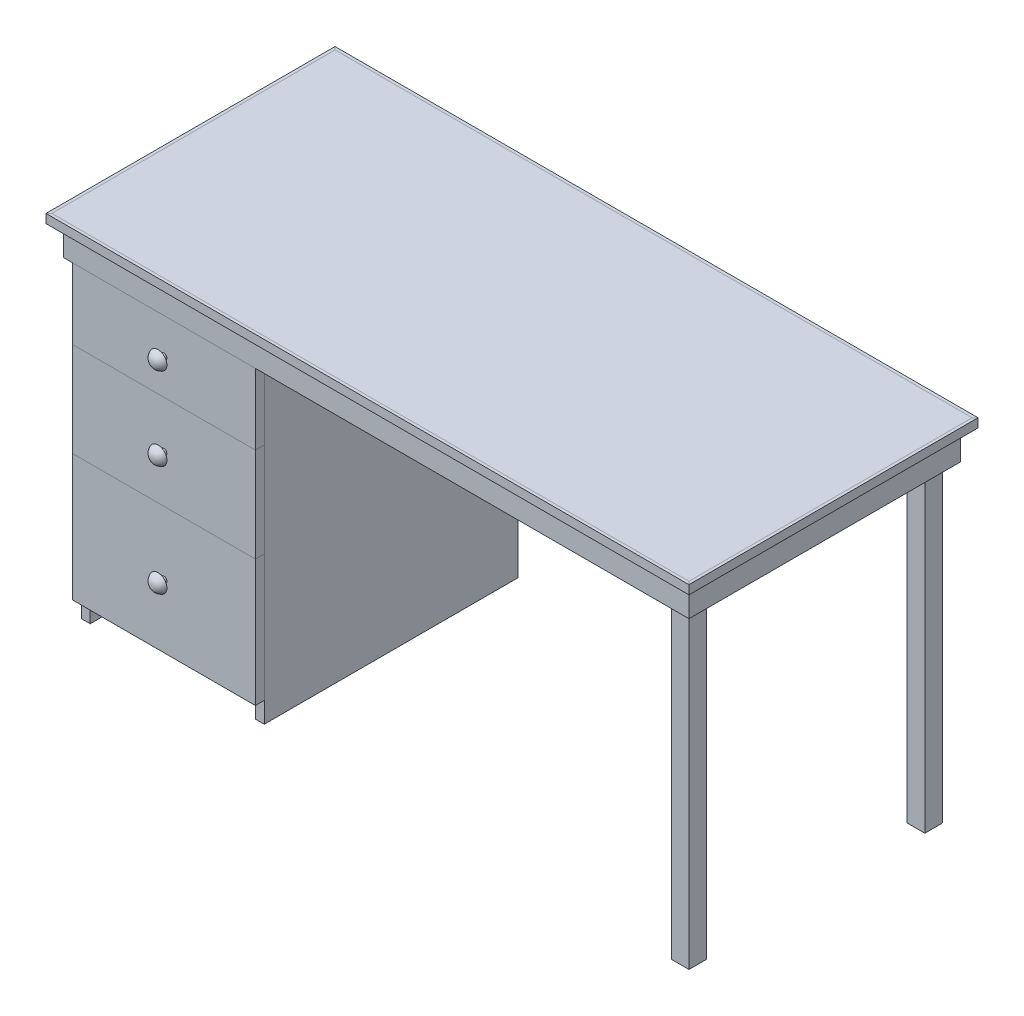
SolidWorks part; units mm, degrees
material "Oak"
ref_plane "Front Plane" through (0, 0, 0) normal (0, 0, 1) x (1, 0, 0)
ref_plane "Top Plane" through (0, 0, 0) normal (0, 1, 0) x (1, 0, 0)
ref_plane "Right Plane" through (0, 0, 0) normal (1, 0, 0) x (0, 0, -1)
sketch "Sketch1" plane through (0, 0, 0) normal (0, 1, 0) x (1, 0, 0)
  line L0 (-685.8, 304.8) -> (685.8, -304.8) construction
  line L1 (-685.8, 304.8) -> (685.8, 304.8)
  line L2 (-685.8, 304.8) -> (-685.8, -304.8)
  line L3 (-685.8, -304.8) -> (685.8, -304.8)
  line L4 (685.8, 304.8) -> (685.8, -304.8)
  dimension "D1" = 609.6
  dimension "D2" = 1371.6
extrude "Top" add sketch "Sketch1" against normal blind 19.05
sketch "Sketch26" plane through (0, 0, 0) normal (0, 1, 0) x (1, 0, 0)
  line L0 (-692.15, -311.15) -> (-685.8, -304.8)
  line L1 (-685.8, -304.8) -> (685.8, -304.8)
  line L2 (685.8, -304.8) -> (692.15, -311.15)
  line L3 (692.15, -311.15) -> (-692.15, -311.15)
  line L5 (-685.8, 304.8) -> (-685.8, -304.8) construction
  line L7 (685.8, -304.8) -> (685.8, 304.8) construction
  line L8 (-685.8, 0) -> (685.8, 0) construction
  line L9 (692.15, 311.15) -> (-692.15, 311.15)
  line L10 (685.8, 304.8) -> (692.15, 311.15)
  line L11 (-685.8, 304.8) -> (685.8, 304.8)
  line L12 (-692.15, 311.15) -> (-685.8, 304.8)
  dimension "D1" = 135
  dimension "D2" = 135
  dimension "D3" = 6.35
extrude "Top Siding Front and Back" add sketch "Sketch26" against normal blind 19.05 separate body
sketch "Sketch27" plane through (0, 0, 0) normal (0, 1, 0) x (1, 0, 0)
  line L0 (-692.15, 311.15) -> (-692.15, -311.15)
  line L1 (-692.15, -311.15) -> (-685.8, -304.8)
  line L2 (-685.8, 304.8) -> (-692.15, 311.15)
  line L3 (0, 311.15) -> (0, -311.15) construction
  line L4 (692.15, 311.15) -> (-692.15, 311.15) construction
  line L5 (-692.15, -311.15) -> (692.15, -311.15) construction
  line L6 (-685.8, 304.8) -> (-685.8, -304.8) construction
  line L7 (-685.8, 304.8) -> (-685.8, -304.8)
  line L8 (685.8, 304.8) -> (685.8, -304.8)
  line L9 (685.8, 304.8) -> (692.15, 311.15)
  line L10 (692.15, -311.15) -> (685.8, -304.8)
  line L11 (692.15, 311.15) -> (692.15, -311.15)
extrude "Top Siding Sides" add sketch "Sketch27" against normal blind 19.05 separate body
sketch "Sketch2" plane through (0, -19.05, 0) normal (0, -1, 0) x (1, 0, 0)
  line L0 (-673.1, 292.1) -> (-654.05, 273.05)
  line L1 (-654.05, 273.05) -> (654.05, 273.05)
  line L2 (654.05, 273.05) -> (673.1, 292.1)
  line L3 (673.1, 292.1) -> (-673.1, 292.1)
  line L4 (-685.8, 304.8) -> (-459.3839, 78.3839) construction
  line L5 (685.8, 304.8) -> (524.6776, 143.6776) construction
  line L6 (-685.8, 304.8) -> (685.8, 304.8) construction
  line L7 (685.8, 304.8) -> (685.8, -304.8) construction
  line L8 (654.05, -273.05) -> (673.1, -292.1)
  line L9 (-673.1, -292.1) -> (-654.05, -273.05)
  line L10 (673.1, -292.1) -> (-673.1, -292.1)
  line L11 (-685.8, 0) -> (685.8, 0) construction
  line L12 (-685.8, -304.8) -> (-685.8, 304.8) construction
  line L13 (-654.05, -273.05) -> (654.05, -273.05)
  dimension "D1" = 1346.2
  dimension "D2" = 19.05
  dimension "D3" = 45
  dimension "D4" = 45
extrude "Long Side Rails" add sketch "Sketch2" along normal blind 63.5 separate body
sketch "Sketch3" plane through (0, -19.05, 0) normal (0, -1, 0) x (1, 0, 0)
  line L0 (0, -304.8) -> (0, 304.8) construction
  line L2 (-685.8, 304.8) -> (685.8, 304.8) construction
  line L3 (685.8, -304.8) -> (-685.8, -304.8) construction
  line L4 (-673.1, 292.1) -> (-654.05, 273.05) construction
  line L5 (-673.1, 292.1) -> (-654.05, 273.05)
  line L6 (-673.1, 292.1) -> (-673.1, -292.1)
  line L7 (-654.05, 273.05) -> (-654.05, -273.05)
  line L9 (-654.05, -273.05) -> (-673.1, -292.1) construction
  line L10 (654.05, -273.05) -> (673.1, -292.1)
  line L11 (673.1, 292.1) -> (673.1, -292.1)
  line L12 (673.1, 292.1) -> (654.05, 273.05)
  line L13 (654.05, 273.05) -> (654.05, -273.05)
  line L14 (-654.05, -273.05) -> (-673.1, -292.1)
extrude "Short Side Rails" add sketch "Sketch3" along normal blind 63.5 separate body
sketch "Sketch4" plane through (0, -19.05, 0) normal (0, -1, 0) x (1, 0, 0)
  line L0 (-685.8, 0) -> (685.8, 0) construction
  line L1 (654.05, 273.05) -> (615.95, 273.05)
  line L2 (654.05, 273.05) -> (654.05, 234.95)
  line L3 (654.05, 234.95) -> (615.95, 234.95)
  line L4 (615.95, 273.05) -> (615.95, 234.95)
  line L5 (-685.8, -304.8) -> (-685.8, 304.8) construction
  line L6 (685.8, 304.8) -> (685.8, -304.8) construction
  line L7 (654.05, -234.95) -> (615.95, -234.95)
  line L8 (654.05, -273.05) -> (654.05, -234.95)
  line L9 (654.05, -273.05) -> (615.95, -273.05)
  line L10 (615.95, -273.05) -> (615.95, -234.95)
  dimension "D1" = 38.1
extrude "Legs" add sketch "Sketch4" along normal blind 736.6
sketch "Sketch5" plane through (0, -19.05, 0) normal (0, -1, 0) x (1, 0, 0)
  line L0 (615.95, -273.05) -> (-654.05, -273.05) construction
  line L1 (-654.05, 273.05) -> (-635, 273.05)
  line L2 (-654.05, 273.05) -> (-654.05, -273.05)
  line L3 (-654.05, -273.05) -> (-635, -273.05)
  line L4 (-635, 273.05) -> (-635, -273.05)
  line L5 (-457.2, 304.8) -> (-457.2, -304.8) construction
  line L6 (-685.8, 304.8) -> (685.8, 304.8) construction
  line L7 (685.8, -304.8) -> (-685.8, -304.8) construction
  line L8 (-260.35, -273.05) -> (-279.4, -273.05)
  line L9 (-260.35, 273.05) -> (-279.4, 273.05)
  line L10 (-260.35, 273.05) -> (-260.35, -273.05)
  line L11 (-279.4, 273.05) -> (-279.4, -273.05)
  dimension "D1" = 19.05
  dimension "D2" = 196.85
extrude "Case Sides" add sketch "Sketch5" along normal blind 736.6 separate body
sketch "Sketch6" plane through (0, -19.05, 0) normal (0, -1, 0) x (1, 0, 0)
  line L4 (-635, -273.05) -> (-635, 273.05) construction
  line L5 (-279.4, 273.05) -> (-279.4, -273.05) construction
  line L7 (-635, -273.05) -> (-635, 273.05)
  line L8 (-279.4, 273.05) -> (-279.4, -273.05)
  line L9 (-635, 273.05) -> (-279.4, 273.05)
  line L10 (-635, -273.05) -> (-279.4, -273.05)
extrude "Case Top" add sketch "Sketch6" along normal blind 19.05 separate body
ref_plane "Case Bottom Plane" through (0, -685.8, 0) normal (0, -1, 0) x (-1, 0, 0)
sketch "Sketch7" plane through (0, -685.8, 0) normal (0, -1, 0) x (-1, 0, 0)
  line L0 (635, -273.05) -> (279.4, -273.05)
  line L1 (279.4, -273.05) -> (279.4, 273.05)
  line L2 (279.4, 273.05) -> (635, 273.05)
  line L3 (635, 273.05) -> (635, -273.05)
extrude "Case Bottom" add sketch "Sketch7" along normal blind 19.05 separate body
sketch "Sketch8" plane through (0, -19.05, 0) normal (0, -1, 0) x (1, 0, 0)
  line L0 (577.85, 273.05) -> (654.05, 196.85)
  line L1 (-654.05, 273.05) -> (615.95, 273.05) construction
  line L2 (654.05, 234.95) -> (654.05, -234.95) construction
  line L3 (550.9092, 273.05) -> (654.05, 169.9092)
  line L4 (577.85, 273.05) -> (550.9092, 273.05)
  line L5 (654.05, 196.85) -> (654.05, 169.9092)
  line L6 (0, 0) -> (685.8, 0) construction
  line L7 (685.8, 304.8) -> (685.8, -304.8) construction
  line L8 (654.05, -196.85) -> (654.05, -169.9092)
  line L9 (550.9092, -273.05) -> (654.05, -169.9092)
  line L10 (577.85, -273.05) -> (550.9092, -273.05)
  line L11 (577.85, -273.05) -> (654.05, -196.85)
  dimension "D1" = 19.05
extrude "Bracing" add sketch "Sketch8" along normal blind 63.5 separate body
sketch "Sketch11" plane through (0, 0, 273.05) normal (0, 0, 1) x (1, 0, 0)
  line L0 (-654.05, -755.65) -> (-654.05, -19.05) construction
  line L1 (-654.05, -82.55) -> (-260.35, -82.55)
  line L2 (-654.05, -82.55) -> (-654.05, -234.95)
  line L3 (-654.05, -234.95) -> (-260.35, -234.95)
  line L4 (-260.35, -82.55) -> (-260.35, -234.95)
  line L5 (-260.35, -755.65) -> (-260.35, -19.05) construction
  line L6 (673.1, -82.55) -> (-673.1, -82.55) construction
  dimension "D1" = 152.4
extrude "Top Drawer Front" add sketch "Sketch11" along normal blind 19.05 separate body
sketch "Sketch12" plane through (0, 0, 273.05) normal (0, 0, 1) x (1, 0, 0)
  line L0 (-260.35, -755.65) -> (-260.35, -19.05) construction
  line L1 (-654.05, -234.95) -> (-260.35, -234.95)
  line L2 (-654.05, -234.95) -> (-654.05, -438.15)
  line L3 (-654.05, -438.15) -> (-260.35, -438.15)
  line L4 (-260.35, -234.95) -> (-260.35, -438.15)
  dimension "D1" = 203.2
extrude "Middle Drawer Front" add sketch "Sketch12" along normal blind 19.05 separate body
sketch "Sketch13" plane through (0, 0, 273.05) normal (0, 0, 1) x (1, 0, 0)
  line L1 (-654.05, -438.15) -> (-260.35, -438.15)
  line L2 (-654.05, -438.15) -> (-654.05, -711.2)
  line L3 (-654.05, -711.2) -> (-260.35, -711.2)
  line L4 (-260.35, -438.15) -> (-260.35, -711.2)
  dimension "D1" = 273.05
extrude "Bottom Drawer Front" add sketch "Sketch13" along normal blind 19.05 separate body
sketch "Sketch14" plane through (0, 0, 273.05) normal (0, 0, 1) x (1, 0, 0)
  line L0 (-609.6, -95.25) -> (-609.6, -215.9)
  line L1 (-622.3, -95.25) -> (-609.6, -95.25)
  line L2 (-622.3, -95.25) -> (-622.3, -234.95)
  line L3 (-622.3, -234.95) -> (-609.6, -234.95)
  line L4 (-609.6, -215.9) -> (-615.95, -215.9)
  line L5 (-615.95, -215.9) -> (-615.95, -222.25)
  line L6 (-615.95, -222.25) -> (-609.6, -222.25)
  line L7 (-609.6, -222.25) -> (-609.6, -234.95)
  line L8 (-635, -755.65) -> (-635, -19.05) construction
  line L9 (673.1, -82.55) -> (-673.1, -82.55) construction
  line L10 (-457.2, 0) -> (-457.2, -729.8008) construction
  line L11 (-622.3, -450.85) -> (-622.3, -679.45)
  line L12 (-622.3, -679.45) -> (-609.6, -679.45)
  line L13 (-609.6, -679.45) -> (-609.6, -666.75)
  line L14 (-609.6, -666.75) -> (-615.95, -666.75)
  line L15 (-615.95, -666.75) -> (-615.95, -660.4)
  line L16 (-615.95, -660.4) -> (-609.6, -660.4)
  line L17 (-609.6, -660.4) -> (-609.6, -450.85)
  line L18 (-609.6, -450.85) -> (-622.3, -450.85)
  line L19 (-622.3, -247.65) -> (-622.3, -438.15)
  line L20 (-622.3, -438.15) -> (-609.6, -438.15)
  line L21 (-609.6, -438.15) -> (-609.6, -425.45)
  line L22 (-609.6, -425.45) -> (-615.95, -425.45)
  line L23 (-615.95, -425.45) -> (-615.95, -419.1)
  line L24 (-615.95, -419.1) -> (-609.6, -419.1)
  line L25 (-609.6, -419.1) -> (-609.6, -247.65)
  line L26 (-609.6, -247.65) -> (-622.3, -247.65)
  line L27 (-304.8, -247.65) -> (-292.1, -247.65)
  line L28 (-304.8, -419.1) -> (-304.8, -247.65)
  line L29 (-298.45, -419.1) -> (-304.8, -419.1)
  line L30 (-298.45, -425.45) -> (-298.45, -419.1)
  line L31 (-304.8, -425.45) -> (-298.45, -425.45)
  line L32 (-304.8, -438.15) -> (-304.8, -425.45)
  line L33 (-292.1, -438.15) -> (-304.8, -438.15)
  line L34 (-292.1, -247.65) -> (-292.1, -438.15)
  line L35 (-304.8, -450.85) -> (-292.1, -450.85)
  line L36 (-304.8, -660.4) -> (-304.8, -450.85)
  line L37 (-298.45, -660.4) -> (-304.8, -660.4)
  line L38 (-298.45, -666.75) -> (-298.45, -660.4)
  line L39 (-304.8, -666.75) -> (-298.45, -666.75)
  line L40 (-304.8, -679.45) -> (-304.8, -666.75)
  line L41 (-292.1, -679.45) -> (-304.8, -679.45)
  line L42 (-292.1, -450.85) -> (-292.1, -679.45)
  line L43 (-304.8, -222.25) -> (-304.8, -234.95)
  line L44 (-298.45, -222.25) -> (-304.8, -222.25)
  line L45 (-298.45, -215.9) -> (-298.45, -222.25)
  line L46 (-304.8, -215.9) -> (-298.45, -215.9)
  line L47 (-292.1, -234.95) -> (-304.8, -234.95)
  line L48 (-292.1, -95.25) -> (-292.1, -234.95)
  line L49 (-292.1, -95.25) -> (-304.8, -95.25)
  line L50 (-304.8, -95.25) -> (-304.8, -215.9)
  dimension "D1" = 12.7
  dimension "D2" = 12.7
  dimension "D3" = 12.7
  dimension "D4" = 6.35
  dimension "D5" = 6.35
  dimension "D6" = 12.7
  dimension "D7" = 139.7
  dimension "D8" = 165.1
  dimension "D9" = 190.5
  dimension "D10" = 12.7
  dimension "D11" = 12.7
  dimension "D12" = 228.6
extrude "All Drawer Sides" add sketch "Sketch14" against normal blind 355.6 separate body
sketch "Sketch17" plane through (-609.6, 0, 0) normal (1, 0, 0) x (0, 0, -1)
  line L0 (-273.05, -95.25) -> (-273.05, -234.95)
  line L1 (-273.05, -234.95) -> (-260.35, -234.95)
  line L2 (82.55, -234.95) -> (-273.05, -234.95) construction
  line L3 (-260.35, -234.95) -> (-260.35, -222.25)
  line L4 (82.55, -222.25) -> (-273.05, -222.25) construction
  line L5 (-260.35, -222.25) -> (-266.7, -222.25)
  line L6 (-266.7, -222.25) -> (-266.7, -215.9)
  line L7 (82.55, -215.9) -> (-273.05, -215.9) construction
  line L8 (-266.7, -215.9) -> (-260.35, -215.9)
  line L9 (-260.35, -215.9) -> (-260.35, -95.25)
  line L10 (82.55, -95.25) -> (-273.05, -95.25) construction
  line L11 (-260.35, -95.25) -> (-273.05, -95.25)
  line L12 (-273.05, -247.65) -> (-260.35, -247.65)
  line L13 (-273.05, -247.65) -> (-273.05, -438.15)
  line L14 (-273.05, -438.15) -> (-260.35, -438.15)
  line L15 (82.55, -438.15) -> (-273.05, -438.15) construction
  line L16 (-260.35, -438.15) -> (-260.35, -425.45)
  line L17 (-260.35, -425.45) -> (-266.7, -425.45)
  line L18 (82.55, -425.45) -> (-273.05, -425.45) construction
  line L19 (-266.7, -425.45) -> (-266.7, -419.1)
  line L20 (-266.7, -419.1) -> (-260.35, -419.1)
  line L21 (-260.35, -419.1) -> (-260.35, -247.65)
  line L22 (-260.35, -450.85) -> (-273.05, -450.85)
  line L23 (82.55, -450.85) -> (-273.05, -450.85) construction
  line L24 (-273.05, -450.85) -> (-273.05, -679.45)
  line L25 (-273.05, -679.45) -> (-260.35, -679.45)
  line L26 (82.55, -679.45) -> (-273.05, -679.45) construction
  line L27 (-260.35, -679.45) -> (-260.35, -666.75)
  line L28 (-260.35, -666.75) -> (-266.7, -666.75)
  line L29 (82.55, -666.75) -> (-273.05, -666.75) construction
  line L30 (-266.7, -666.75) -> (-266.7, -660.4)
  line L31 (82.55, -660.4) -> (-273.05, -660.4) construction
  line L32 (-266.7, -660.4) -> (-260.35, -660.4)
  line L33 (-260.35, -660.4) -> (-260.35, -450.85)
  line L34 (-95.25, -95.25) -> (-95.25, -753.1612) construction
  line L35 (69.85, -660.4) -> (69.85, -450.85)
  line L36 (76.2, -660.4) -> (69.85, -660.4)
  line L37 (76.2, -666.75) -> (76.2, -660.4)
  line L38 (69.85, -666.75) -> (76.2, -666.75)
  line L39 (69.85, -679.45) -> (69.85, -666.75)
  line L40 (82.55, -679.45) -> (69.85, -679.45)
  line L41 (82.55, -450.85) -> (82.55, -679.45)
  line L42 (69.85, -450.85) -> (82.55, -450.85)
  line L43 (69.85, -419.1) -> (69.85, -247.65)
  line L44 (76.2, -419.1) -> (69.85, -419.1)
  line L45 (76.2, -425.45) -> (76.2, -419.1)
  line L46 (69.85, -425.45) -> (76.2, -425.45)
  line L47 (69.85, -438.15) -> (69.85, -425.45)
  line L48 (82.55, -438.15) -> (69.85, -438.15)
  line L49 (82.55, -247.65) -> (82.55, -438.15)
  line L50 (82.55, -247.65) -> (69.85, -247.65)
  line L51 (69.85, -95.25) -> (82.55, -95.25)
  line L52 (69.85, -215.9) -> (69.85, -95.25)
  line L53 (76.2, -215.9) -> (69.85, -215.9)
  line L54 (76.2, -222.25) -> (76.2, -215.9)
  line L55 (69.85, -222.25) -> (76.2, -222.25)
  line L56 (69.85, -234.95) -> (69.85, -222.25)
  line L57 (82.55, -234.95) -> (69.85, -234.95)
  line L58 (82.55, -95.25) -> (82.55, -234.95)
  dimension "D1" = 6.35
  dimension "D2" = 12.7
  dimension "D3" = 177.8
extrude "All Drawer Front and Back" add sketch "Sketch17" along normal blind 304.8 separate body
sketch "Sketch22" plane through (0, 0, 266.7) normal (0, 0, -1) x (-1, 0, 0)
  line L0 (304.8, -222.25) -> (609.6, -222.25) construction
  line L1 (304.8, -215.9) -> (609.6, -215.9) construction
  line L2 (304.8, -222.25) -> (609.6, -222.25)
  line L3 (304.8, -215.9) -> (609.6, -215.9)
  line L4 (304.8, -215.9) -> (298.45, -215.9)
  line L5 (298.45, -215.9) -> (298.45, -222.25)
  line L6 (304.8, -222.25) -> (298.45, -222.25)
  line L7 (609.6, -215.9) -> (615.95, -215.9)
  line L8 (615.95, -215.9) -> (615.95, -222.25)
  line L9 (615.95, -222.25) -> (609.6, -222.25)
  line L10 (304.8, -425.45) -> (609.6, -425.45) construction
  line L11 (304.8, -419.1) -> (609.6, -419.1) construction
  line L12 (304.8, -425.45) -> (609.6, -425.45)
  line L13 (304.8, -419.1) -> (609.6, -419.1)
  line L14 (304.8, -660.4) -> (609.6, -660.4) construction
  line L15 (304.8, -660.4) -> (609.6, -660.4)
  line L16 (304.8, -666.75) -> (609.6, -666.75) construction
  line L17 (304.8, -666.75) -> (609.6, -666.75)
  line L18 (609.6, -419.1) -> (615.95, -419.1)
  line L19 (615.95, -419.1) -> (615.95, -425.45)
  line L20 (615.95, -425.45) -> (609.6, -425.45)
  line L21 (304.8, -419.1) -> (298.45, -419.1)
  line L22 (298.45, -419.1) -> (298.45, -425.45)
  line L23 (298.45, -425.45) -> (304.8, -425.45)
  line L24 (609.6, -660.4) -> (615.95, -660.4)
  line L25 (615.95, -660.4) -> (615.95, -666.75)
  line L26 (615.95, -666.75) -> (609.6, -666.75)
  line L27 (304.8, -660.4) -> (298.45, -660.4)
  line L28 (298.45, -660.4) -> (298.45, -666.75)
  line L29 (298.45, -666.75) -> (304.8, -666.75)
extrude "All Drawer Bottoms" add sketch "Sketch22" along normal blind 342.9 separate body
ref_plane "Drawer Knob Plane" through (-457.2, 0, 0) normal (1, 0, 0) x (0, 0, -1)
sketch "Sketch28" plane through (-457.2, 0, 0) normal (1, 0, 0) x (0, 0, -1)
  line L0 (-273.05, -755.65) -> (-273.05, -19.05) construction
  line L1 (-304.8, -152.4) -> (-292.1, -152.4)
  line L2 (-304.8, -152.4) -> (-304.8, -139.7)
  line L3 (-292.1, -158.75) -> (-317.5, -158.75)
  line L4 (-292.1, -152.4) -> (-292.1, -158.75)
  line L5 (-292.1, -82.55) -> (-273.05, -82.55) construction
  arc A0 (-304.8, -139.7) -> (-317.5, -158.75) centre (-298.4806, -157.6713) ccw
  dimension "D6" = 19.05
  dimension "D1" = 19.05
  dimension "D2" = 12.7
  dimension "D3" = 12.7
  dimension "D4" = 25.4
  dimension "D5" = 6.35
  dimension "D7" = 76.2
revolve "Top Drawer Knob" add sketch "Sketch28" angle 360 about L3
sketch "Sketch29" plane through (-457.2, 0, 0) normal (1, 0, 0) x (0, 0, -1)
  line L0 (-292.1, -330.2) -> (-304.8, -330.2)
  line L1 (-292.1, -330.2) -> (-292.1, -336.55)
  line L2 (-292.1, -336.55) -> (-317.5, -336.55)
  line L3 (-304.8, -330.2) -> (-304.8, -317.5)
  line L4 (-273.05, -755.65) -> (-273.05, -19.05) construction
  line L6 (-292.1, -234.95) -> (-273.05, -234.95) construction
  arc A0 (-317.5, -336.55) -> (-304.8, -317.5) centre (-298.4806, -335.4713) cw
  dimension "D4" = 19.05
  dimension "D1" = 19.05
  dimension "D2" = 12.7
  dimension "D3" = 12.7
  dimension "D5" = 25.4
  dimension "D6" = 6.35
  dimension "D7" = 101.6
revolve "Middle Drawer Knob" add sketch "Sketch29" angle 360 about L2
sketch "Sketch30" plane through (-457.2, 0, 0) normal (1, 0, 0) x (0, 0, -1)
  line L0 (-292.1, -568.325) -> (-304.8, -568.325)
  line L1 (-304.8, -568.325) -> (-304.8, -555.625)
  line L2 (-292.1, -568.325) -> (-292.1, -574.675)
  line L3 (-317.5, -574.675) -> (-292.1, -574.675)
  line L4 (-273.05, -755.65) -> (-273.05, -19.05) construction
  line L5 (-292.1, -438.15) -> (-273.05, -438.15) construction
  arc A0 (-317.5, -574.675) -> (-304.8, -555.625) centre (-298.4806, -573.5963) cw
  point P8 (-282.575, -438.15)
  dimension "D1" = 19.05
  dimension "D2" = 6.35
  dimension "D3" = 25.4
  dimension "D4" = 12.7
  dimension "D5" = 12.7
  dimension "D6" = 19.05
  dimension "D7" = 136.525
revolve "Bottom Drawer Knob" add sketch "Sketch30" angle 360 about L3
sketch "Sketch31" plane through (0, 0, 273.05) normal (0, 0, -1) x (-1, 0, 0)
  line L0 (260.35, -234.95) -> (654.05, -234.95) construction
  line L1 (292.1, -222.25) -> (279.4, -222.25)
  line L2 (279.4, -222.25) -> (279.4, -234.95)
  line L3 (279.4, -234.95) -> (292.1, -234.95)
  line L4 (292.1, -222.25) -> (292.1, -234.95)
  line L5 (292.1, -234.95) -> (292.1, -95.25) construction
  line L6 (635, -222.25) -> (635, -234.95)
  line L7 (279.4, -425.45) -> (292.1, -425.45)
  line L8 (292.1, -425.45) -> (292.1, -438.15)
  line L9 (292.1, -438.15) -> (279.4, -438.15)
  line L10 (279.4, -425.45) -> (279.4, -438.15)
  line L12 (279.4, -666.75) -> (292.1, -666.75)
  line L13 (292.1, -666.75) -> (292.1, -679.45)
  line L14 (279.4, -679.45) -> (292.1, -679.45)
  line L15 (279.4, -666.75) -> (279.4, -679.45)
  line L16 (260.35, -438.15) -> (654.05, -438.15) construction
  line L18 (304.8, -679.45) -> (609.6, -679.45) construction
  line L19 (635, -666.75) -> (635, -679.45)
  line L20 (635, -679.45) -> (622.3, -679.45)
  line L21 (622.3, -666.75) -> (622.3, -679.45)
  line L22 (635, -666.75) -> (622.3, -666.75)
  line L23 (635, -425.45) -> (635, -438.15)
  line L24 (622.3, -438.15) -> (635, -438.15)
  line L25 (622.3, -425.45) -> (622.3, -438.15)
  line L26 (635, -425.45) -> (622.3, -425.45)
  line L27 (622.3, -222.25) -> (622.3, -234.95)
  line L28 (635, -234.95) -> (622.3, -234.95)
  line L29 (622.3, -222.25) -> (635, -222.25)
  dimension "D1" = 12.7
  dimension "D2" = 12.7
  dimension "D3" = 12.7
  dimension "D4" = 12.7
extrude "Sliding Rails" add sketch "Sketch31" along normal blind 355.6 separate body
